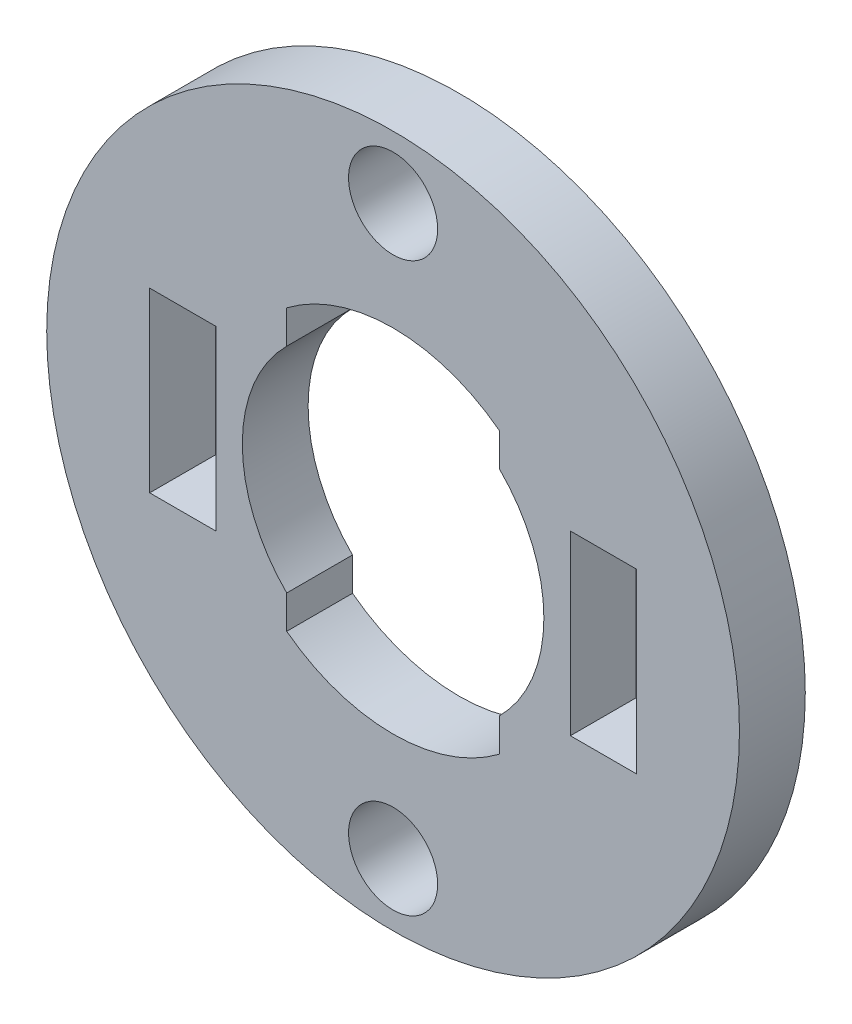
SolidWorks part; units mm, degrees
ref_plane "Front Plane" through (0, 0, 0) normal (0, 0, 1) x (1, 0, 0)
ref_plane "Top Plane" through (0, 0, 0) normal (0, 1, 0) x (1, 0, 0)
ref_plane "Right Plane" through (0, 0, 0) normal (1, 0, 0) x (0, 0, -1)
sketch "Sketch1" plane through (0, 0, 0) normal (0, 0, 1) x (1, 0, 0)
  circle A0 centre (0, 0) radius 15.5067
  point P0 (0, 0)
  dimension "D3" = 31.0134
extrude "Boss-Extrude1" add sketch "Sketch1" along normal blind 2.9464
sketch "Sketch2" plane through (0, 0, 2.9464) normal (0, 0, 1) x (1, 0, 0)
  line L0 (0, 0) -> (0, 10.2775) construction
  line L1 (4.7625, 6.2704) -> (4.7625, 4.7834)
  line L2 (-4.7625, 6.2704) -> (-4.7625, 4.7834)
  line L3 (-1.3314, 0) -> (4.8348, 0) construction
  line L4 (4.7625, -6.2704) -> (4.7625, -4.7834)
  line L5 (-4.7625, -6.2704) -> (-4.7625, -4.7834)
  arc A0 (-4.7625, 4.7834) -> (-4.7625, -4.7834) centre (0, 0) ccw
  arc A1 (4.7625, 6.2704) -> (-4.7625, 6.2704) centre (0, 0) ccw
  arc A2 (4.7625, -6.2704) -> (-4.7625, -6.2704) centre (0, 0) cw
  arc A3 (4.7625, -4.7834) -> (4.7625, 4.7834) centre (0, 0) ccw
  dimension "D1" = 6.75
  dimension "D3" = 9.525
  dimension "D2" = 7.874
extrude "Cut-Extrude1" cut sketch "Sketch2" against normal up to next
sketch "Sketch3" plane through (0, 0, 0) normal (0, 0, -1) x (-1, 0, 0)
  line L1 (-10.8966, 3.9687) -> (-7.9375, 3.9687)
  line L2 (-10.8966, 3.9687) -> (-10.8966, -3.9688)
  line L3 (-10.8966, -3.9688) -> (-7.9375, -3.9688)
  line L4 (-7.9375, 3.9687) -> (-7.9375, -3.9688)
  line L5 (-10.8966, 3.9687) -> (-7.9375, -3.9688) construction
  line L6 (-10.8966, -3.9688) -> (-7.9375, 3.9687) construction
  line L7 (0, 1.3883) -> (0, -1.2397) construction
  point P0 (-9.4171, 0)
  dimension "D1" = 7.9375
  dimension "D2" = 2.9591
  dimension "D3" = 15.875
extrude "Cut-Extrude2" cut sketch "Sketch3" against normal up to next
sketch "Sketch4" plane through (0, 0, 0) normal (0, 0, -1) x (-1, 0, 0)
  line L0 (-10.8966, 3.9687) -> (-10.8966, -3.9688) construction
  line L1 (-10.8966, -3.9688) -> (-7.9375, -3.9688) construction
  circle A0 centre (-7.9375, 3.9687) radius 0.635
  circle A1 centre (-7.9375, -3.9688) radius 0.635
  circle A2 centre (-10.8966, 3.9687) radius 0.635
  circle A3 centre (-10.8966, -3.9688) radius 0.635
  dimension "D1" = 1.27
extrude "Cut-Extrude3" [suppressed] cut sketch "Sketch4" against normal up to next
mirror "Mirror1" about plane through (0, 0, 0) normal (1, 0, 0) of "Cut-Extrude3", "Cut-Extrude2"
hole_wizard "Tap Drill for #4 Helicoil1" positions "Sketch7" profile "Sketch6" hole size "#4-40" standard "ANSI Inch" end condition up to next
sketch "Sketch7" plane through (0, 0, 2.9464) normal (0, 0, 1) x (1, 0, 0)
  line L0 (0, -12.7) -> (0, 12.7) construction
  point P0 (0, 12.7)
  point P5 (0, -12.7)
  dimension "D1" = 25.4
sketch "Sketch6" plane through (0, 12.7, 2.9464) normal (1, 0, 0) x (0, -1, 0)
  line L0 (0, 0) -> (0, 2.9464)
  line L1 (0, 2.9464) -> (1.9939, 2.9464)
  line L2 (1.9939, 2.9464) -> (1.9939, 0)
  line L5 (1.9939, 0) -> (0, 0)
  line L11 (0, -6.35) -> (0, 107.95) construction
  dimension "Thru Hole Dia." = 3.9878
  dimension "Thru Hole Depth" = 2.9464
